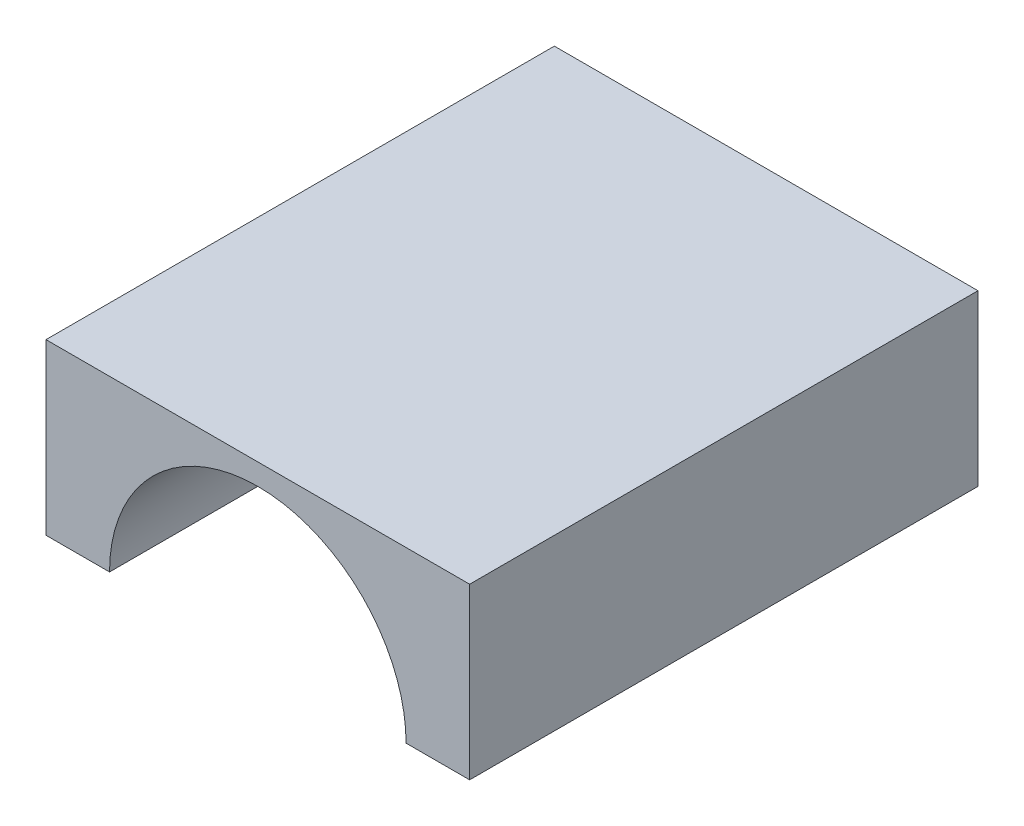
SolidWorks part; units mm, degrees
ref_plane "Front Plane" through (0, 0, 0) normal (0, 0, 1) x (1, 0, 0)
ref_plane "Top Plane" through (0, 0, 0) normal (0, 1, 0) x (1, 0, 0)
ref_plane "Right Plane" through (0, 0, 0) normal (1, 0, 0) x (0, 0, -1)
sketch "Sketch1" plane through (0, 0, 0) normal (0, 1, 0) x (1, 0, 0)
  line L1 (-10, -12) -> (10, -12)
  line L2 (-10, -12) -> (-10, 12)
  line L3 (-10, 12) -> (10, 12)
  line L4 (10, -12) -> (10, 12)
  line L5 (-10, -12) -> (10, 12) construction
  line L6 (-10, 12) -> (10, -12) construction
  point P0 (0, 0)
extrude "Boss-Extrude1" add sketch "Sketch1" along normal blind 8
sketch "Sketch2" plane through (0, 0, 12) normal (0, 0, 1) x (1, 0, 0)
  line L0 (-10, 0) -> (10, 0) construction
  circle A0 centre (0, 0) radius 7
extrude "Cut-Extrude1" cut sketch "Sketch2" against normal blind 22
sketch "Sketch3" plane through (0, 0, -12) normal (0, 0, -1) x (-1, 0, 0)
  line L0 (-10, 0) -> (10, 0) construction
  line L3 (-2, -6.7082) -> (-2, -5)
  line L4 (-2, -5) -> (2, -5)
  line L5 (2, -6.7082) -> (2, -5)
  line L6 (-2, -9) -> (2, -5) construction
  line L7 (-2, -5) -> (2, -9) construction
  arc A0 (2, -6.7082) -> (-2, -6.7082) centre (0, 0) ccw
  point P4 (0, -7)
extrude "Boss-Extrude2" add sketch "Sketch3" against normal blind 2
